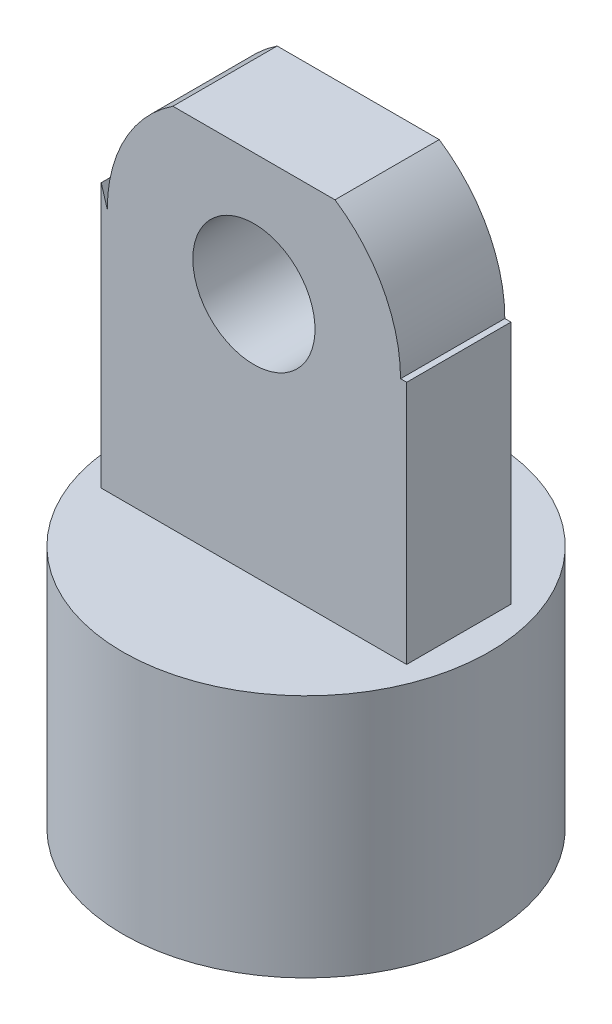
SolidWorks part; units mm, degrees
ref_plane "Front Plane" through (0, 0, 0) normal (0, 0, 1) x (1, 0, 0)
ref_plane "Top Plane" through (0, 0, 0) normal (0, 1, 0) x (1, 0, 0)
ref_plane "Right Plane" through (0, 0, 0) normal (1, 0, 0) x (0, 0, -1)
sketch "Sketch1" plane through (0, 0, 0) normal (0, 1, 0) x (1, 0, 0)
  circle A0 centre (0, 0) radius 15
  dimension "D1" = 30
extrude "Boss-Extrude1" add sketch "Sketch1" along normal blind 20
sketch "Sketch2" plane through (0, 0, 0) normal (0, -1, 0) x (1, 0, 0)
  circle A0 centre (0, 0) radius 7.5
  dimension "D1" = 15
extrude "Cut-Extrude1" cut sketch "Sketch2" against normal blind 10
sketch "Sketch3" plane through (0, 20, 0) normal (0, 1, 0) x (1, 0, 0)
  line L1 (12.5, -4.267) -> (-12.5, -4.267)
  line L2 (12.5, -4.267) -> (12.5, 4.267)
  line L3 (12.5, 4.267) -> (-12.5, 4.267)
  line L4 (-12.5, -4.267) -> (-12.5, 4.267)
  line L5 (12.5, -4.267) -> (-12.5, 4.267) construction
  line L6 (12.5, 4.267) -> (-12.5, -4.267) construction
  point P0 (0, 0)
  dimension "D1" = 25
extrude "Boss-Extrude2" add sketch "Sketch3" along normal blind 30
sketch "Sketch4" plane through (0, 0, -4.267) normal (0, 0, -1) x (-1, 0, 0)
  line L0 (0, 50) -> (0, 20) construction
  line L1 (-12.5, 50) -> (12.5, 50) construction
  line L2 (-12.5, 20) -> (12.5, 20) construction
  line L3 (12, 112.8468) -> (20.6996, 68.6404)
  line L4 (12, 112.8468) -> (-15.7044, 112.8468)
  line L5 (20.6996, 68.6404) -> (12, 40)
  line L6 (-12, 40) -> (-18.3469, 40)
  line L7 (-18.3469, 40) -> (-15.7044, 112.8468)
  circle A0 centre (0, 40) radius 5
  arc A1 (12, 40) -> (-12, 40) centre (0, 40) ccw
  point P16 (0, 0)
  dimension "D1" = 10
  dimension "D3" = 12
  dimension "D2" = 10
extrude "Cut-Extrude2" cut sketch "Sketch4" against normal blind 30
sketch "Sketch5" plane through (0, 10, 0) normal (0, -1, 0) x (1, 0, 0)
  circle A1 centre (0, 0) radius 7.5
  circle A2 centre (0, 0) radius 7.5
  dimension "D1" = 0
extrude "Boss-Extrude3" add sketch "Sketch5" along normal blind 15
